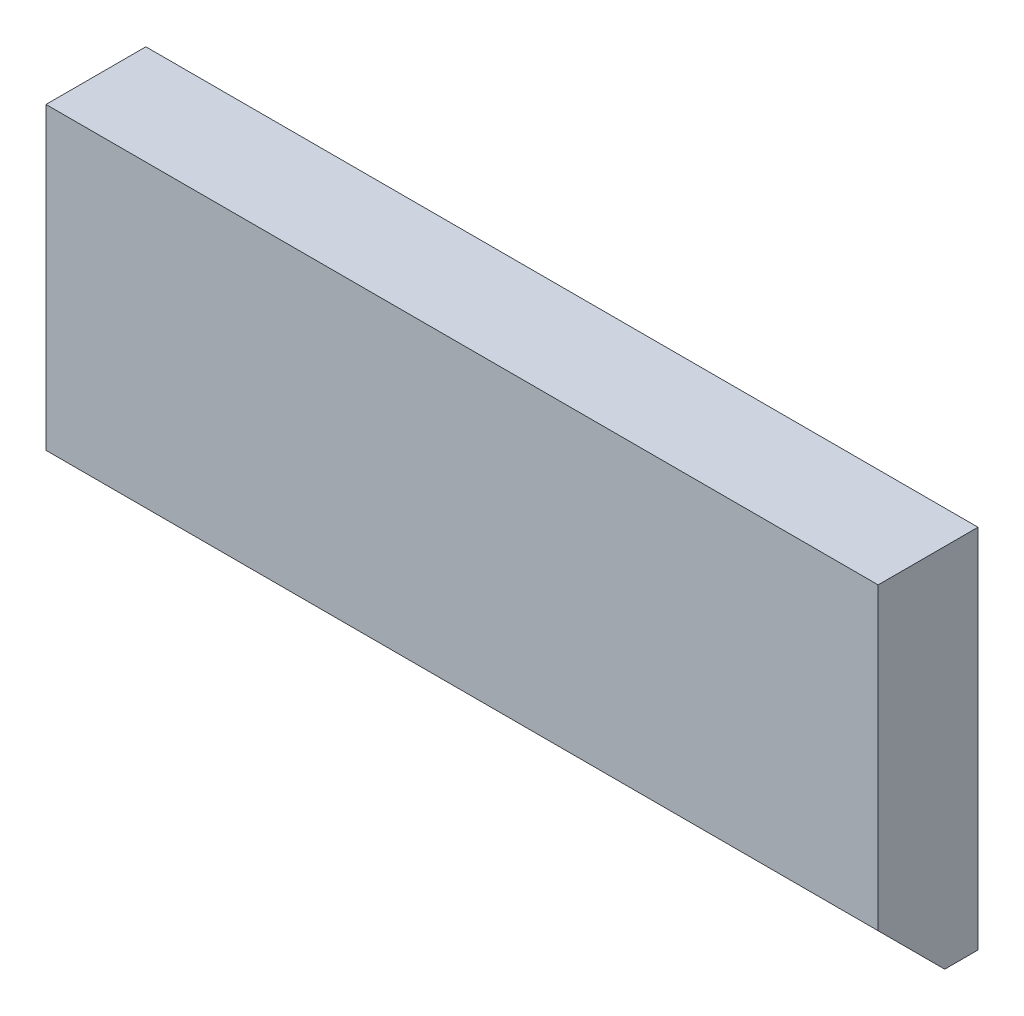
SolidWorks part; units mm, degrees
material "Стекло"
ref_plane "Front" through (0, 0, 0) normal (0, 0, 1) x (1, 0, 0)
ref_plane "Top" through (0, 0, 0) normal (0, 1, 0) x (1, 0, 0)
ref_plane "Right" through (0, 0, 0) normal (1, 0, 0) x (0, 0, -1)
sketch "Эскиз1" plane through (0, 0, 0) normal (0, 0, 1) x (1, 0, 0)
  line L1 (-13, -5.5) -> (12, -5.5)
  line L2 (-13, -5.5) -> (-13, 5.5)
  line L3 (-13, 5.5) -> (12, 5.5)
  line L4 (12, -5.5) -> (12, 5.5)
  dimension "D1" = 25
  dimension "D2" = 11
  dimension "D3" = 5.5
  dimension "D4" = 12
extrude "Вытянуть1" add sketch "Эскиз1" along normal blind 3
chamfer "Фаска3" distance 2 angle 45 1 edges at (-0.5, -5.5, 3)
chamfer "Фаска2" [suppressed] distance 0.3 angle 45
